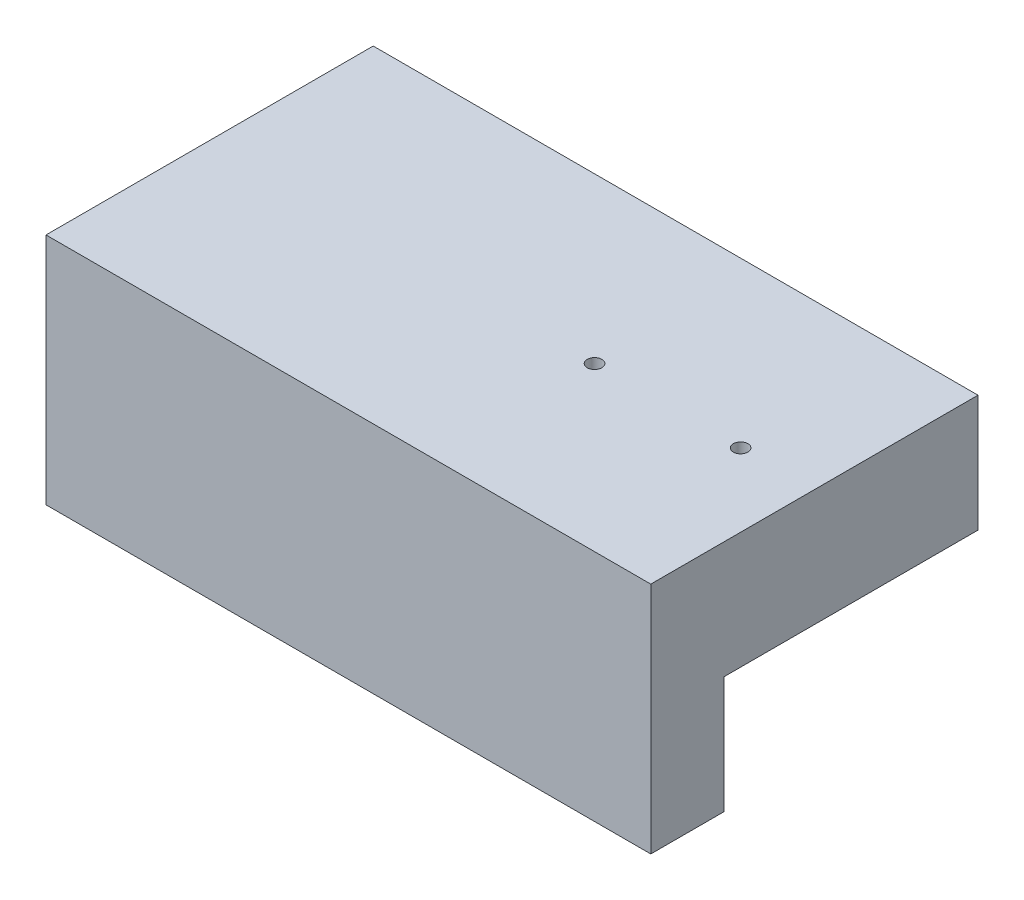
SolidWorks part; units mm, degrees
ref_plane "Front Plane" through (0, 0, 0) normal (0, 0, 1) x (1, 0, 0)
ref_plane "Top Plane" through (0, 0, 0) normal (0, 1, 0) x (1, 0, 0)
ref_plane "Right Plane" through (0, 0, 0) normal (1, 0, 0) x (0, 0, -1)
sketch "Sketch1" plane through (0, 26.5957, 0) normal (0, 1, 0) x (1, 0, 0)
  line L0 (-11.2695, -19.7651) -> (-11.2695, -30.8141) construction
  line L1 (15.0195, -19.7651) -> (-11.2695, -19.7651)
  line L2 (15.0195, -19.7651) -> (15.0195, -33.9891)
  line L3 (15.0195, -33.9891) -> (-11.2695, -33.9891)
  line L4 (-11.2695, -19.7651) -> (-11.2695, -33.9891)
  line L5 (15.0195, -30.8141) -> (-9.682, -30.8141) construction
  dimension "D1" = 3.175
extrude "Boss-Extrude2" add sketch "Sketch1" along normal blind 5.08
sketch "Sketch2" plane through (0, 26.5957, 0) normal (0, -1, 0) x (1, 0, 0)
  line L0 (-11.2695, 30.8141) -> (-11.2695, 33.9891)
  line L1 (-11.2695, 19.7651) -> (-11.2695, 33.9891) construction
  line L2 (-9.682, 30.8141) -> (-11.2695, 30.8141) construction
  line L3 (-11.2695, 33.9891) -> (15.0195, 33.9891)
  line L4 (15.0195, 33.9891) -> (15.0195, 30.8141)
  line L5 (15.0195, 33.9891) -> (15.0195, 19.7651) construction
  line L6 (15.0195, 30.8141) -> (0.859, 30.8141)
  line L7 (15.0195, 30.8141) -> (-9.682, 30.8141) construction
  line L8 (0.859, 30.8141) -> (0.859, 32.4016)
  line L9 (0.859, 32.4016) -> (-4.221, 32.4016)
  line L10 (-4.221, 32.4016) -> (-4.221, 30.8141)
  line L11 (-4.221, 30.8141) -> (-11.2695, 30.8141)
  line L12 (3.526, 29.2266) -> (-6.888, 29.2266) construction
  line L13 (-1.681, 29.2266) -> (-1.681, 33.9891) construction
  point P24 (0.859, 30.8141)
  point P25 (15.0195, 31.8011)
  dimension "D1" = 5.08
  dimension "D2" = 1.5875
  dimension "D3" = 3.175
extrude "Boss-Extrude3" add sketch "Sketch2" along normal blind 5.08
sketch "Sketch3" plane through (0, 26.5957, 0) normal (0, -1, 0) x (1, 0, 0)
  line L0 (-4.221, 30.8141) -> (-4.221, 32.4016) construction
  line L1 (-4.221, 32.4016) -> (0.859, 32.4016) construction
  line L2 (0.859, 32.4016) -> (0.859, 30.8141) construction
  line L3 (-4.221, 30.8141) -> (-4.221, 32.4016)
  line L4 (-4.221, 32.4016) -> (0.859, 32.4016)
  line L5 (0.859, 32.4016) -> (0.859, 30.8141)
  line L6 (3.526, 21.3526) -> (3.526, 30.8141)
  line L7 (0.859, 30.8141) -> (15.0195, 30.8141) construction
  line L8 (3.526, 30.8141) -> (0.859, 30.8141)
  line L9 (3.526, 21.3526) -> (-6.888, 21.3526)
  line L10 (3.526, 21.3526) -> (-9.682, 21.3526) construction
  line L11 (-6.888, 21.3526) -> (-6.888, 30.8141)
  line L12 (-11.2695, 30.8141) -> (-4.221, 30.8141) construction
  line L13 (-6.888, 30.8141) -> (-4.221, 30.8141)
  line L14 (-11.2695, 19.7651) -> (-11.2695, 30.8141) construction
  dimension "D1" = 4.3815
extrude "Cut-Extrude1" cut sketch "Sketch3" against normal blind 3.4925
sketch "Sketch4" plane through (0, 31.6757, 0) normal (0, 1, 0) x (1, 0, 0)
  line L0 (15.0195, -33.9891) -> (15.0195, -19.7651) construction
  line L1 (15.0195, -19.7651) -> (-11.2695, -19.7651) construction
  circle A0 centre (5.4945, -26.9089) radius 0.3175
  circle A1 centre (11.8445, -26.9089) radius 0.3175
  point P4 (0, 0)
  dimension "D1" = 6.35
  dimension "D2" = 0.635
  dimension "D3" = 3.175
  dimension "D4" = 7.1437
extrude "Cut-Extrude2" cut sketch "Sketch4" against normal up to next
